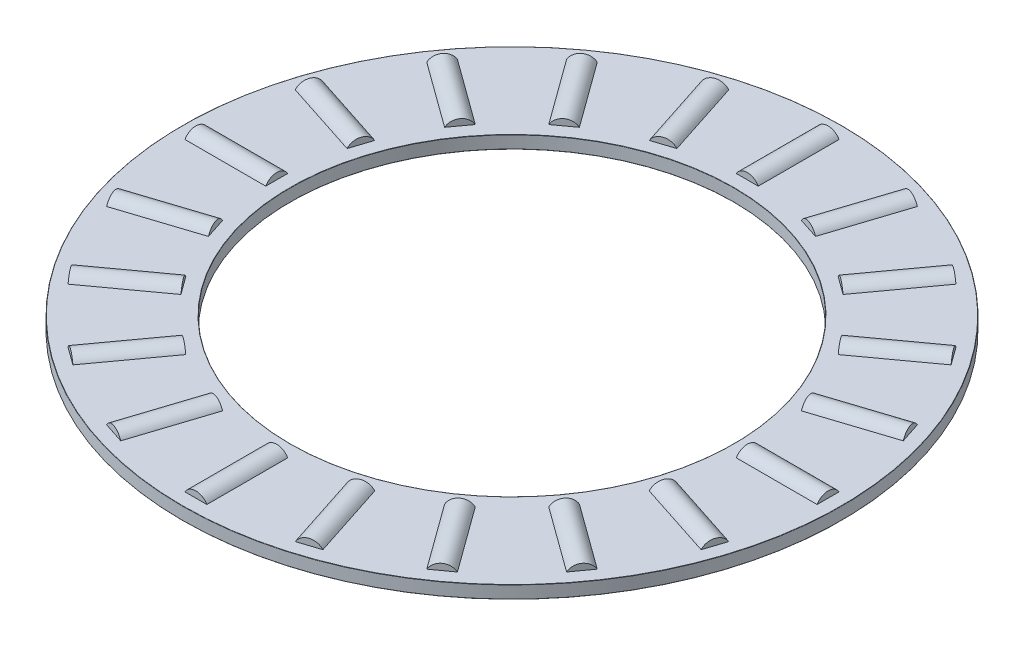
SolidWorks part; units mm, degrees
ref_plane "Front Plane" through (0, 0, 0) normal (0, 0, 1) x (1, 0, 0)
ref_plane "Top Plane" through (0, 0, 0) normal (0, 1, 0) x (1, 0, 0)
ref_plane "Right Plane" through (0, 0, 0) normal (1, 0, 0) x (0, 0, -1)
sketch "Sketch1" plane through (0, 0, 0) normal (1, 0, 0) x (0, 0, -1)
  line L0 (-26, 0) -> (26, 0) construction
  line L1 (0, -1) -> (0, 1) construction
  line L2 (-26, 0.5) -> (-17.5, 0.5)
  line L3 (-26, 0.5) -> (-26, -0.5)
  line L4 (-26, -0.5) -> (-17.5, -0.5)
  line L5 (-17.5, 0.5) -> (-17.5, -0.5)
  line L7 (-21.75, 1) -> (-21.75, 0.5) construction
  line L8 (-24.9375, 1) -> (-18.5625, 1) construction
  line L9 (-24.9375, 1) -> (-24.9375, -1) construction
  line L10 (-24.9375, -1) -> (-18.5625, -1) construction
  line L11 (-18.5625, 1) -> (-18.5625, -1) construction
  point P16 (-24.9375, 0)
  dimension "OD" = 52
  dimension "Shaft Dia" = 35
  dimension "Th" = 2
  dimension "D2" = 1
  dimension "D1" = 6.375
  dimension "D3" = 8.5
revolve "Revolve1" add sketch "Sketch1" angle 360 about L1
sketch "Sketch3" plane through (0, 0, 0) normal (1, 0, 0) x (0, 0, -1)
  line L0 (-24.9375, 1) -> (-24.9375, -1) construction
  line L1 (-24.9375, 0) -> (-18.5625, 0)
  line L2 (-24.9375, 0) -> (-24.9375, 1)
  line L3 (-24.9375, 1) -> (-18.5625, 1)
  line L4 (-18.5625, 0) -> (-18.5625, 1)
revolve "Cut-Revolve1" cut sketch "Sketch3" angle 360 about L1
sketch "Sketch2" plane through (0, 0, 0) normal (1, 0, 0) x (0, 0, -1)
  line L1 (-24.9375, 0) -> (-18.5625, 0)
  line L2 (-24.9375, 0) -> (-24.9375, 1)
  line L3 (-24.9375, 1) -> (-18.5625, 1)
  line L4 (-18.5625, 0) -> (-18.5625, 1)
revolve "Revolve2" add sketch "Sketch2" angle 360 about L1
ref_axis "Axis1" through (0, 1, 0) along (0, -1, 0)
pattern_circular "CirPattern1" count 20 every 18 about axis through (0, 1, 0) along (0, -1, 0) of bodies 187 411
pattern_circular "CirPattern2" count 20 every 18 about axis through (0, 0, 0) along (0, 1, 0) of "Cut-Revolve1"
sketch "Sketch4" plane through (0, 0, 0) normal (1, 0, 0) x (0, 0, -1)
  line L0 (-26, 0.5) -> (-26, -0.5) construction
  line L1 (-26, 9) -> (-17.5, 9)
  line L2 (-26, 9) -> (-26, 10)
  line L3 (-26, 10) -> (-17.5, 10)
  line L4 (-17.5, 9) -> (-17.5, 10)
  line L5 (-26, -10) -> (-17.5, -10)
  line L6 (-26, -10) -> (-26, -9)
  line L7 (-26, -9) -> (-17.5, -9)
  line L8 (-17.5, -10) -> (-17.5, -9)
  line L10 (-17.5, 0.5) -> (-17.5, -0.5) construction
  line L11 (0, 0) -> (-26, 0) construction
  line L12 (-26, 0) -> (26, 0) construction
  line L13 (0, -1) -> (0, 1) construction
  dimension "Ht" = 20
  dimension "Washer Th" = 1
  dimension "Washer ID" = 35
  dimension "Washer OD" = 52
revolve "Revolve3" [suppressed] add sketch "Sketch4" angle 360 about L1
fillet "Fillet1" [suppressed] radius 0.02
fillet "Fillet2" radius 0.02 4 edges at (0, -0.5, -17.5) (0, 0.5, -17.5) (0, -0.5, -26) (0, 0.5, -26)
fillet "Fillet3" [suppressed] radius 0.02
equation "\"D2@Sketch1\" = \"Th@Sketch1\"*.5"
equation "\"D1@Fillet1\" = \"Th@Sketch1\"*.01"
equation "\"D1@Fillet2\" = \"D1@Fillet1\""
equation "\"D1@Fillet3\" = \"D1@Fillet1\""
equation "\"D1@Sketch1\" = \"D3@Sketch1\"*.75"
equation "\"Angle@CirPattern1\" = 360/\"Rollers@CirPattern1\""
equation "\"Rollers@CirPattern1\" = \"OD@Sketch1\"*.375"
equation "\"D1@CirPattern2\" = \"Rollers@CirPattern1\""
equation "\"D2@CirPattern2\" = \"Angle@CirPattern1\""
equation "\"Ht@Sketch4\" = \"Th@Sketch1\"*10"
